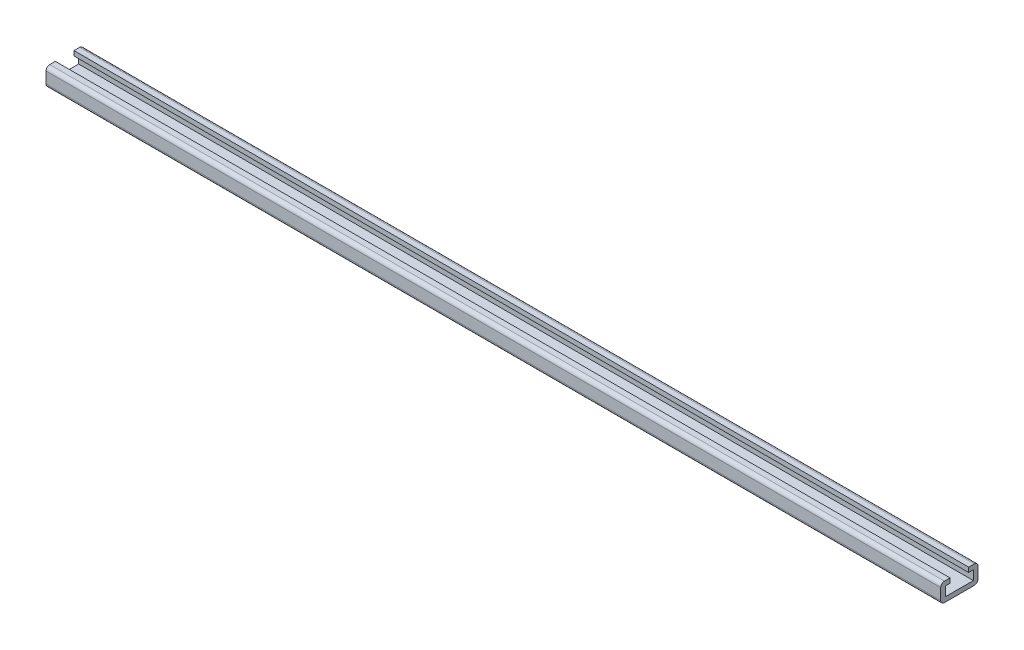
SolidWorks part; units mm, degrees
material "Plain Carbon Steel"
ref_plane "Front Plane" through (0, 0, 0) normal (0, 0, 1) x (1, 0, 0)
ref_plane "Top Plane" through (0, 0, 0) normal (0, 1, 0) x (1, 0, 0)
ref_plane "Right Plane" through (0, 0, 0) normal (1, 0, 0) x (0, 0, -1)
sketch "Sketch1" plane through (0, 0, 0) normal (1, 0, 0) x (0, 0, -1)
  line L12 (0, 0) -> (-12.7, 0)
  line L13 (-12.7, 0) -> (-12.7, 12.7)
  line L14 (-12.7, 12.7) -> (-6.35, 12.7)
  line L15 (-6.35, 12.7) -> (-6.35, 9.525)
  line L16 (-6.35, 9.525) -> (-9.525, 9.525)
  line L17 (-9.525, 9.525) -> (-9.525, 3.175)
  line L18 (-9.525, 3.175) -> (0, 3.175)
  line L19 (0, 3.175) -> (0, 0)
  dimension "D1" = 12.7
  dimension "D2" = 12.7
  dimension "D3" = 3.175
  dimension "D4" = 3.175
  dimension "D5" = 3.175
  dimension "D6" = 6.35
extrude "Boss-Extrude1" add sketch "Sketch1" along normal blind 609.6
mirror "Mirror1" about plane through (609.6, 3.175, 0) normal (0, 0, 1) of "Boss-Extrude1"
fillet "Fillet1" radius 2.54 4 edges at (304.8, 0, 12.7) (304.8, 12.7, -12.7) (304.8, 0, -12.7) (304.8, 12.7, 12.7)
hole_wizard "1/4 Clearance Hole1" positions "Sketch2" profile "Sketch3" hole size "1/4" standard "ANSI Inch"
sketch "Sketch2" plane through (0, 3.175, 0) normal (0, 1, 0) x (1, 0, 0)
  line L0 (609.6, 9.525) -> (609.6, -9.525) construction
  point P0 (25.4, 0)
  point P6 (533.4, 0)
  point P9 (0, 0)
  dimension "D1" = 25.4
  dimension "D2" = 76.2
sketch "Sketch3" plane through (25.4, 3.175, 0) normal (1, 0, 0) x (0, 0, 1)
  line L0 (0, 0) -> (0, 24.3131)
  line L1 (0, 24.3131) -> (3.2639, 22.352)
  line L2 (3.2639, 22.352) -> (3.2639, 0)
  line L5 (3.2639, 0) -> (0, 0)
  line L10 (0, 24.3131) -> (-3.2639, 22.352) construction
  line L11 (0, -6.35) -> (0, 107.95) construction
  dimension "Hole Dia." = 6.5278
  dimension "Hole Depth" = 22.352
  dimension "Drill Angle" = 118
